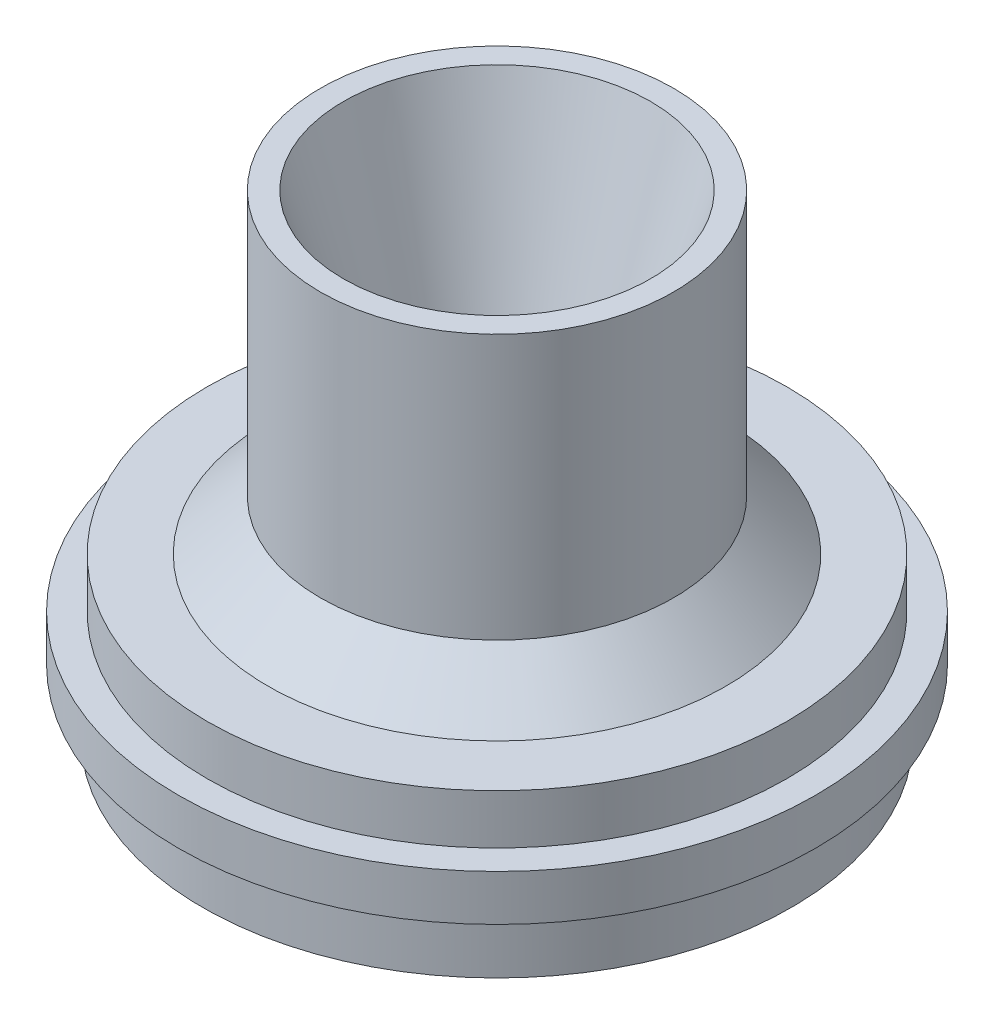
SolidWorks part; units mm, degrees
material "Graphite AR-12"
ref_plane "Front Plane" through (0, 0, 0) normal (0, 0, 1) x (1, 0, 0)
ref_plane "Top Plane" through (0, 0, 0) normal (0, 1, 0) x (1, 0, 0)
ref_plane "Right Plane" through (0, 0, 0) normal (1, 0, 0) x (0, 0, -1)
sketch "Sketch1" plane through (0, 0, 0) normal (0, 0, 1) x (1, 0, 0)
  line L0 (0, 0) -> (0, 25.4) construction
  line L1 (0, 25.4) -> (-22.098, 25.4) construction
  line L2 (-22.098, 25.4) -> (-12.2555, -7.366)
  line L3 (-12.2555, -7.366) -> (-12.2555, -30.226)
  line L4 (-35.0647, -42.8244) -> (-42.3186, -42.8244)
  line L5 (-42.3186, -42.8244) -> (-42.3186, -33.6804)
  line L6 (-42.3186, -33.6804) -> (-45.8216, -33.6804)
  line L7 (-45.8216, -33.6804) -> (-45.8216, -27.0764)
  line L8 (-45.8216, -27.0764) -> (-41.6941, -27.0764)
  line L9 (-41.6941, -27.0764) -> (-41.6941, -19.939)
  line L10 (-41.6941, -19.939) -> (-32.9311, -19.939)
  line L11 (-32.9311, -19.939) -> (-25.4, -12.7)
  line L12 (-25.4, -12.7) -> (-25.4, 25.4)
  line L13 (-25.4, 25.4) -> (-22.098, 25.4)
  line L14 (-12.2555, -30.226) -> (-35.0647, -42.8244)
  dimension "D1" = 25.4
  dimension "D2" = 35.0647
  dimension "D3" = 22.098
  dimension "D4" = 45.8216
  dimension "D5" = 41.6941
  dimension "D6" = 7.1374
  dimension "D7" = 6.604
  dimension "D8" = 9.144
  dimension "D9" = 38.1
  dimension "D10" = 8.763
  dimension "D11" = 7.2539
  dimension "D12" = 12.2555
  dimension "D13" = 32.766
  dimension "D14" = 7.239
  dimension "D15" = 25.4
  dimension "D16" = 22.86
revolve "Revolve1" add sketch "Sketch1" angle 360 about L0
